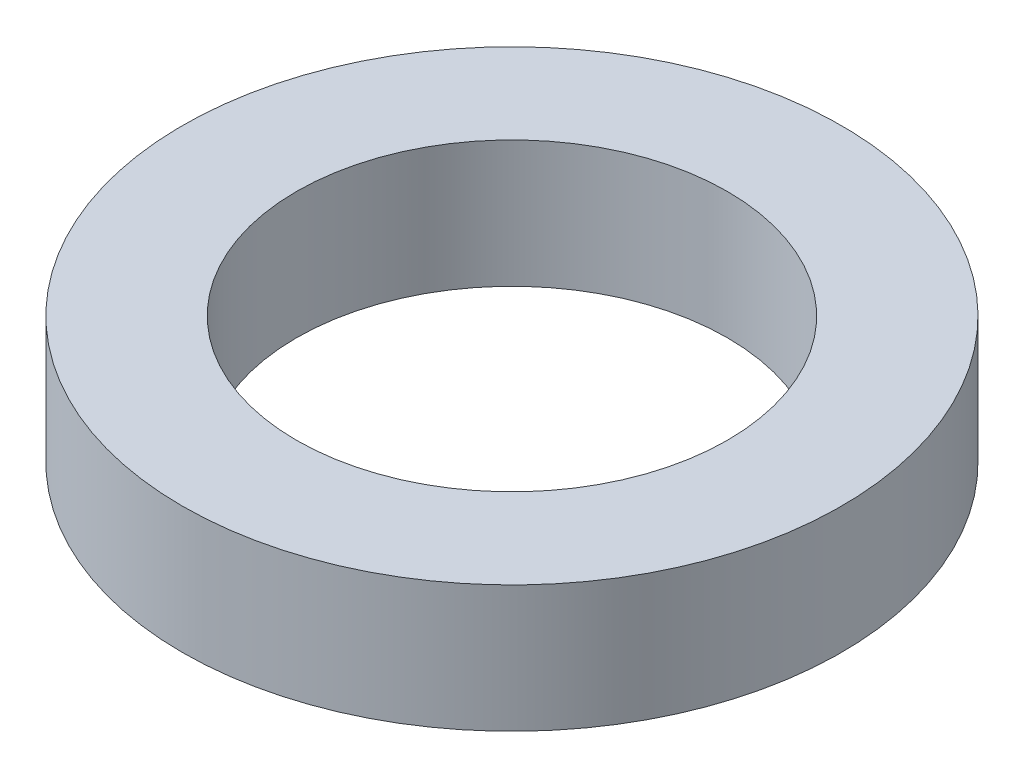
SolidWorks part; units mm, degrees
material "不锈钢 (铁素体)"
ref_plane "前视基准面" through (0, 0, 0) normal (0, 0, 1) x (1, 0, 0)
ref_plane "上视基准面" through (0, 0, 0) normal (0, 1, 0) x (1, 0, 0)
ref_plane "右视基准面" through (0, 0, 0) normal (1, 0, 0) x (0, 0, -1)
sketch "草图1" plane through (0, 0, 0) normal (0, 1, 0) x (1, 0, 0)
  circle A0 centre (0, 0) radius 13
  circle A1 centre (0, 0) radius 8.5
  dimension "D1" = 17
  dimension "D2" = 26
extrude "凸台-拉伸1" add sketch "草图1" along normal blind 5
